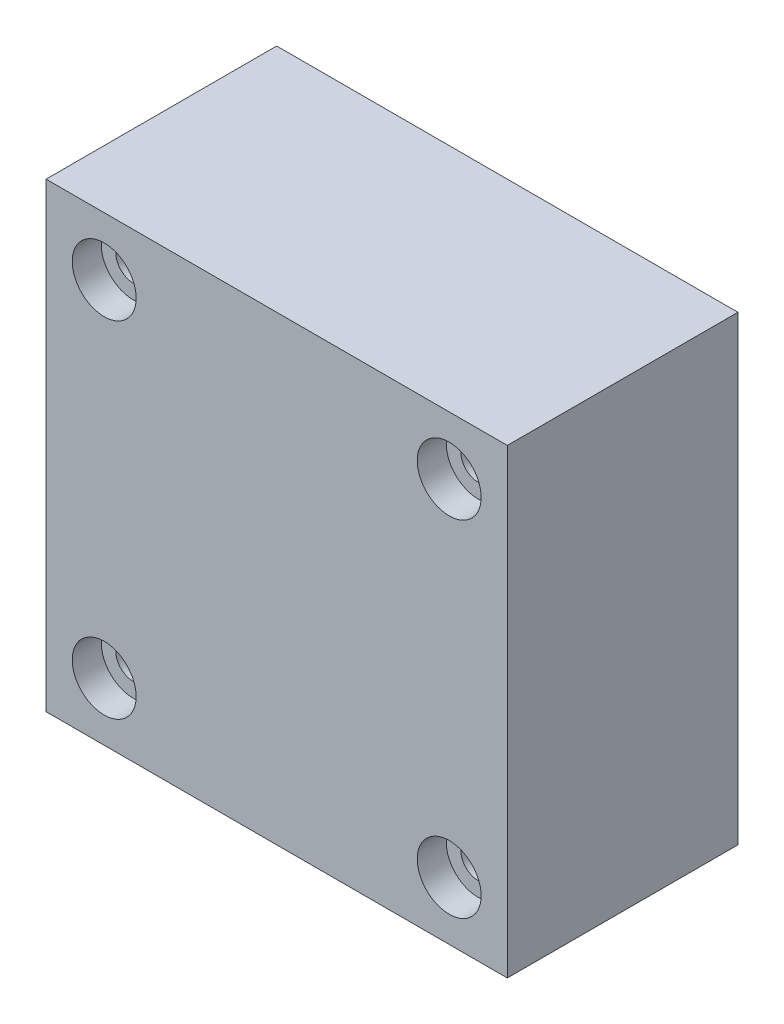
SolidWorks part; units mm, degrees
material "1060 Alloy"
ref_plane "Front Plane" through (0, 0, 0) normal (0, 0, 1) x (1, 0, 0)
ref_plane "Top Plane" through (0, 0, 0) normal (0, 1, 0) x (1, 0, 0)
ref_plane "Right Plane" through (0, 0, 0) normal (1, 0, 0) x (0, 0, -1)
sketch "Sketch1" plane through (0, 0, 0) normal (0, 0, 1) x (1, 0, 0)
  line L1 (-15.875, -15.875) -> (15.875, -15.875)
  line L2 (-15.875, -15.875) -> (-15.875, 15.875)
  line L3 (-15.875, 15.875) -> (15.875, 15.875)
  line L4 (15.875, -15.875) -> (15.875, 15.875)
  line L5 (-15.875, -15.875) -> (15.875, 15.875) construction
  line L6 (-15.875, 15.875) -> (15.875, -15.875) construction
  point P0 (0, 0)
  dimension "D1" = 31.75
  dimension "D2" = 31.75
extrude "Boss-Extrude1" add sketch "Sketch1" along normal mid plane 15.875
hole_wizard "CBORE for M2 SHCS1" positions "Sketch3" profile "Sketch4" counterbore size "M2" standard "ANSI Metric" end condition through all
sketch "Sketch3" plane through (0, 0, 7.9375) normal (0, 0, 1) x (1, 0, 0)
  line L0 (-11.875, 11.875) -> (-11.875, -11.875) construction
  line L1 (-11.875, -11.875) -> (11.875, -11.875) construction
  line L2 (11.875, -11.875) -> (11.875, 11.875) construction
  line L3 (11.875, 11.875) -> (-11.875, 11.875) construction
  line L5 (15.875, 15.875) -> (-15.875, 15.875) construction
  line L6 (-15.875, -15.875) -> (15.875, -15.875) construction
  line L7 (-15.875, 15.875) -> (-15.875, -15.875) construction
  line L8 (15.875, -15.875) -> (15.875, 15.875) construction
  point P0 (-11.875, 11.875)
  point P2 (11.875, 11.875)
  point P4 (11.875, -11.875)
  point P6 (-11.875, -11.875)
  dimension "D1" = 4
  dimension "D2" = 4
  dimension "D3" = 4
  dimension "D4" = 4
sketch "Sketch4" plane through (-11.875, 11.875, 7.9375) normal (1, 0, 0) x (0, -1, 0)
  line L0 (0, 0) -> (0, 15.875)
  line L1 (0, 15.875) -> (1.2, 15.875)
  line L3 (1.2, 15.875) -> (1.2, 2)
  line L4 (1.2, 2) -> (2.2, 2)
  line L5 (2.2, 2) -> (2.2, 0)
  line L7 (2.2, 0) -> (0, 0)
  line L11 (0, -6.35) -> (0, 107.95) construction
  dimension "Thru Hole Dia." = 2.4
  dimension "Thru Hole Depth" = 15.875
  dimension "C'Bore Dia." = 4.4
  dimension "C'Bore Depth" = 2
